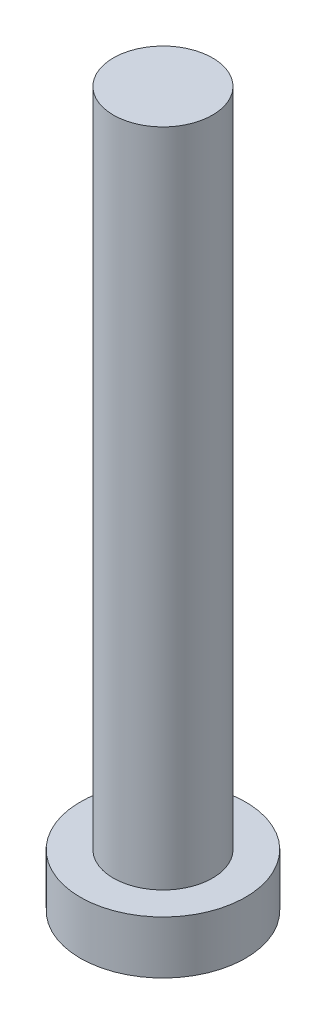
SolidWorks part; units mm, degrees
ref_plane "前视基准面" through (0, 0, 0) normal (0, 0, 1) x (1, 0, 0)
ref_plane "上视基准面" through (0, 0, 0) normal (0, 1, 0) x (1, 0, 0)
ref_plane "右视基准面" through (0, 0, 0) normal (1, 0, 0) x (0, 0, -1)
sketch "草图1" plane through (0, 0, 0) normal (0, 1, 0) x (1, 0, 0)
  circle A0 centre (0, 0) radius 2.5
extrude "凸台-拉伸1" add sketch "草图1" along normal blind 1.6
sketch "草图2" plane through (0, 1.6, 0) normal (0, 1, 0) x (1, 0, 0)
  circle A0 centre (0, 0) radius 1.5
extrude "凸台-拉伸2" add sketch "草图2" along normal blind 20
sketch "草图3" plane through (0, 0, 0) normal (0, -1, 0) x (1, 0, 0)
  line L0 (-0.5, 1) -> (-0.5, 1.75)
  line L1 (-1.75, -0.5) -> (-1, -0.5)
  line L2 (-1.75, -0.5) -> (-1.75, 0.5)
  line L3 (-1.75, 0.5) -> (-1, 0.5)
  line L4 (1.75, -0.5) -> (1.75, 0.5)
  line L5 (-1.75, -0.5) -> (1.75, 0.5) construction
  line L6 (-1.75, 0.5) -> (1.75, -0.5) construction
  line L7 (-0.5, -1.75) -> (0.5, -1.75)
  line L8 (-0.5, -1.75) -> (-0.5, -1)
  line L9 (-0.5, 1.75) -> (0.5, 1.75)
  line L10 (0.5, -1.75) -> (0.5, -1)
  line L11 (-0.5, -1.75) -> (0.5, 1.75) construction
  line L12 (-0.5, 1.75) -> (0.5, -1.75) construction
  line L13 (1, -0.5) -> (1.75, -0.5)
  line L14 (0.5, 1) -> (0.5, 1.75)
  line L15 (1, 0.5) -> (1.75, 0.5)
  arc A0 (1, -0.5) -> (0.5, -1) centre (1, -1) ccw
  arc A1 (-0.5, -1) -> (-1, -0.5) centre (-1, -1) ccw
  arc A2 (0.5, 1) -> (1, 0.5) centre (1, 1) ccw
  arc A3 (-0.5, 1) -> (-1, 0.5) centre (-1, 1) cw
  point P0 (0, 0)
  point P6 (0, 0)
  point P21 (0.5, 0.5)
  dimension "D1" = 0.5
extrude "切除-拉伸1" cut sketch "草图3" against normal blind 1
